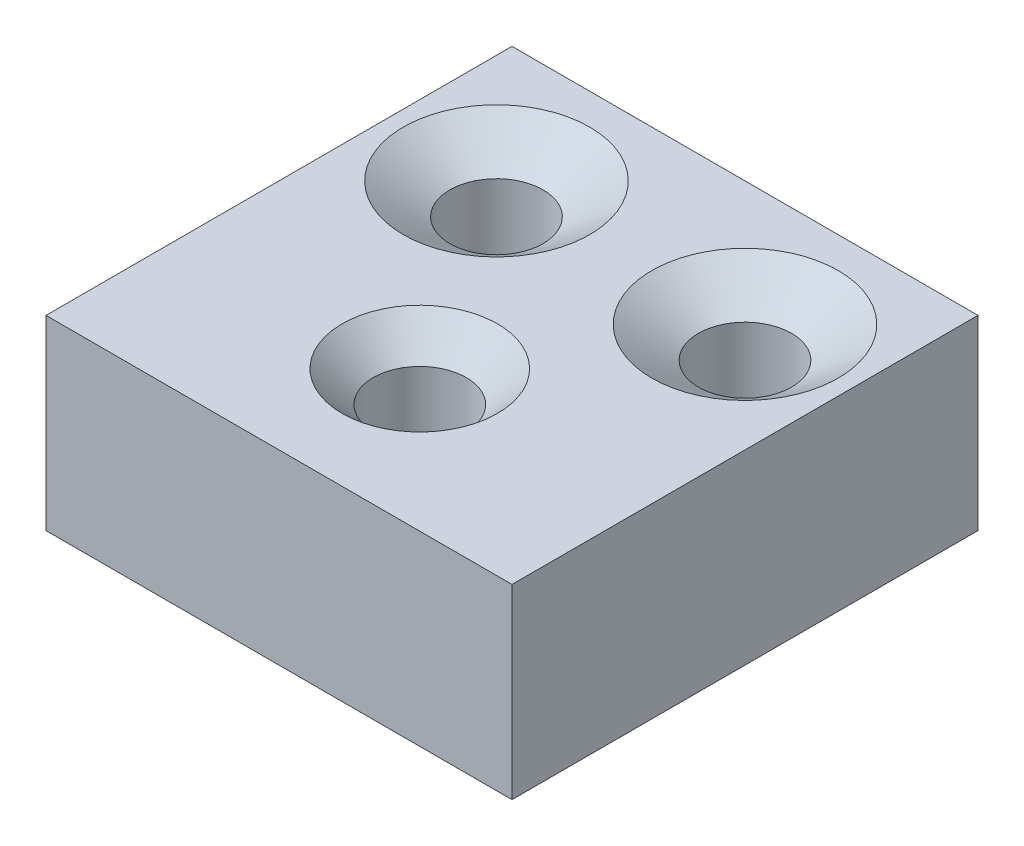
SolidWorks part; units mm, degrees
ref_plane "Front Plane" through (0, 0, 0) normal (0, 0, 1) x (1, 0, 0)
ref_plane "Top Plane" through (0, 0, 0) normal (0, 1, 0) x (1, 0, 0)
ref_plane "Right Plane" through (0, 0, 0) normal (1, 0, 0) x (0, 0, -1)
sketch "Sketch1" plane through (0, 0, 0) normal (0, 1, 0) x (1, 0, 0)
  line L1 (-75, -40) -> (75, -40)
  line L2 (-75, -40) -> (-75, 40)
  line L3 (-75, 40) -> (75, 40)
  line L4 (75, -40) -> (75, 40)
  line L5 (-75, -40) -> (75, 40) construction
  line L6 (-75, 40) -> (75, -40) construction
  point P0 (0, 0)
  dimension "D1" = 80
  dimension "D2" = 150
extrude "Boss-Extrude1" add sketch "Sketch1" along normal blind 60
sketch "Sketch2" plane through (0, 0, 0) normal (0, 0, 1) x (1, 0, 0)
  line L0 (0, 60) -> (-40, 60) construction
  line L1 (-75, 60) -> (75, 60) construction
  line L2 (-40, 60) -> (-70, 60)
  line L3 (-70, 60) -> (-55, 50)
  line L4 (-55, 50) -> (-55, 10)
  line L5 (-55, 10) -> (-40, 10)
  line L6 (-40, 10) -> (-40, 60)
  dimension "D1" = 50
  dimension "D2" = 10
  dimension "D3" = 15
  dimension "D4" = 40
  dimension "D5" = 30
revolve "Cut-Revolve1" cut sketch "Sketch2" angle 360 about L6
mirror "Mirror1" about plane through (0, 0, 0) normal (1, 0, 0) of "Cut-Revolve1"
sketch "Sketch3" plane through (0, 0, 40) normal (0, 0, 1) x (1, 0, 0)
  line L1 (-75, 60) -> (75, 60)
  line L2 (-75, 60) -> (-75, 0)
  line L3 (-75, 0) -> (75, 0)
  line L4 (75, 60) -> (75, 0)
extrude "Boss-Extrude2" add sketch "Sketch3" along normal blind 70
sketch "Sketch4" plane through (0, 60, 0) normal (0, 1, 0) x (1, 0, 0)
  line L0 (-40, 0) -> (40, 0) construction
  line L1 (0, 0) -> (0, -65) construction
  dimension "D1" = 65
ref_plane "Plane1" through (0, 0, 0) normal (1, 0, 0) x (0, 0, -1)
sketch "Sketch6" plane through (0, 0, 0) normal (1, 0, 0) x (0, 0, -1)
  line L0 (-64.6789, 60) -> (-64.6789, 10)
  line L1 (0, 60) -> (-65, 60) construction
  line L2 (-110, 60) -> (40, 60) construction
  line L3 (-64.6789, 10) -> (-79.6789, 10)
  line L4 (-79.6789, 10) -> (-79.6789, 50)
  line L5 (-79.6789, 50) -> (-89.6789, 60)
  line L6 (-89.6789, 60) -> (-64.6789, 60)
  dimension "D1" = 50
  dimension "D2" = 15
  dimension "D3" = 40
  dimension "D4" = 25
revolve "Cut-Revolve2" cut sketch "Sketch6" angle 360 about L0
